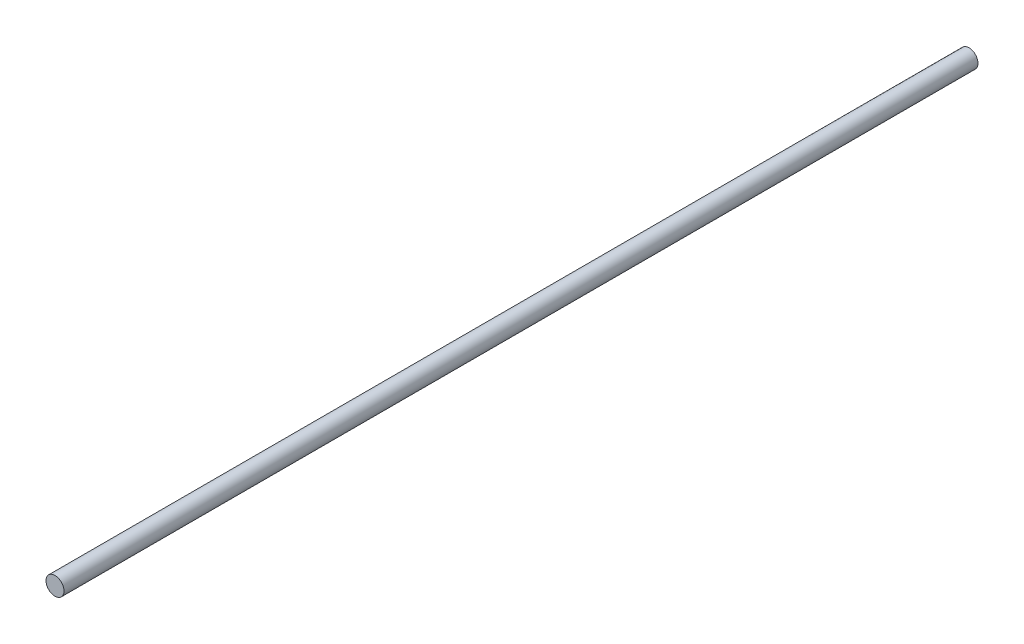
SolidWorks part; units mm, degrees
ref_plane "Ön Düzlem" through (0, 0, 0) normal (0, 0, 1) x (1, 0, 0)
ref_plane "Üst Düzlem" through (0, 0, 0) normal (0, 1, 0) x (1, 0, 0)
ref_plane "Sağ Düzlem" through (0, 0, 0) normal (1, 0, 0) x (0, 0, -1)
sketch "Çizim1" plane through (0, 0, 0) normal (0, 0, 1) x (1, 0, 0)
  circle A0 centre (0, 0) radius 6
  point P3 (0, 0)
  dimension "D1" = 12
extrude "Yükseklik-Ekstrüzyon1" add sketch "Çizim1" along normal blind 609
